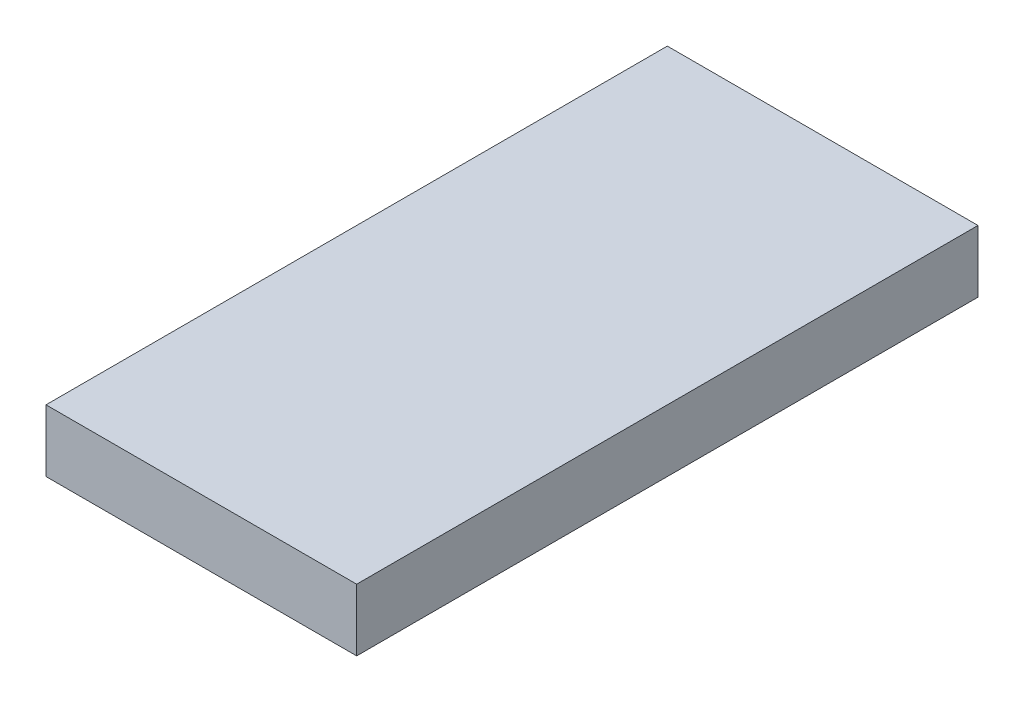
SolidWorks part; units mm, degrees
ref_plane "Front Plane" through (0, 0, 0) normal (0, 0, 1) x (1, 0, 0)
ref_plane "Top Plane" through (0, 0, 0) normal (0, 1, 0) x (1, 0, 0)
ref_plane "Right Plane" through (0, 0, 0) normal (1, 0, 0) x (0, 0, -1)
sketch "Sketch1" plane through (0, 0, 0) normal (0, 0, 1) x (1, 0, 0)
  line L1 (-0.4869, 0.8751) -> (4.5131, 0.8751)
  line L2 (-0.4869, 0.8751) -> (-0.4869, -0.1249)
  line L3 (-0.4869, -0.1249) -> (4.5131, -0.1249)
  line L4 (4.5131, 0.8751) -> (4.5131, -0.1249)
sketch "Sketch2" plane through (0, 0, 0) normal (0, 0, 1) x (1, 0, 0)
extrude "Boss-Extrude1" add sketch "Sketch1" along normal blind 10
